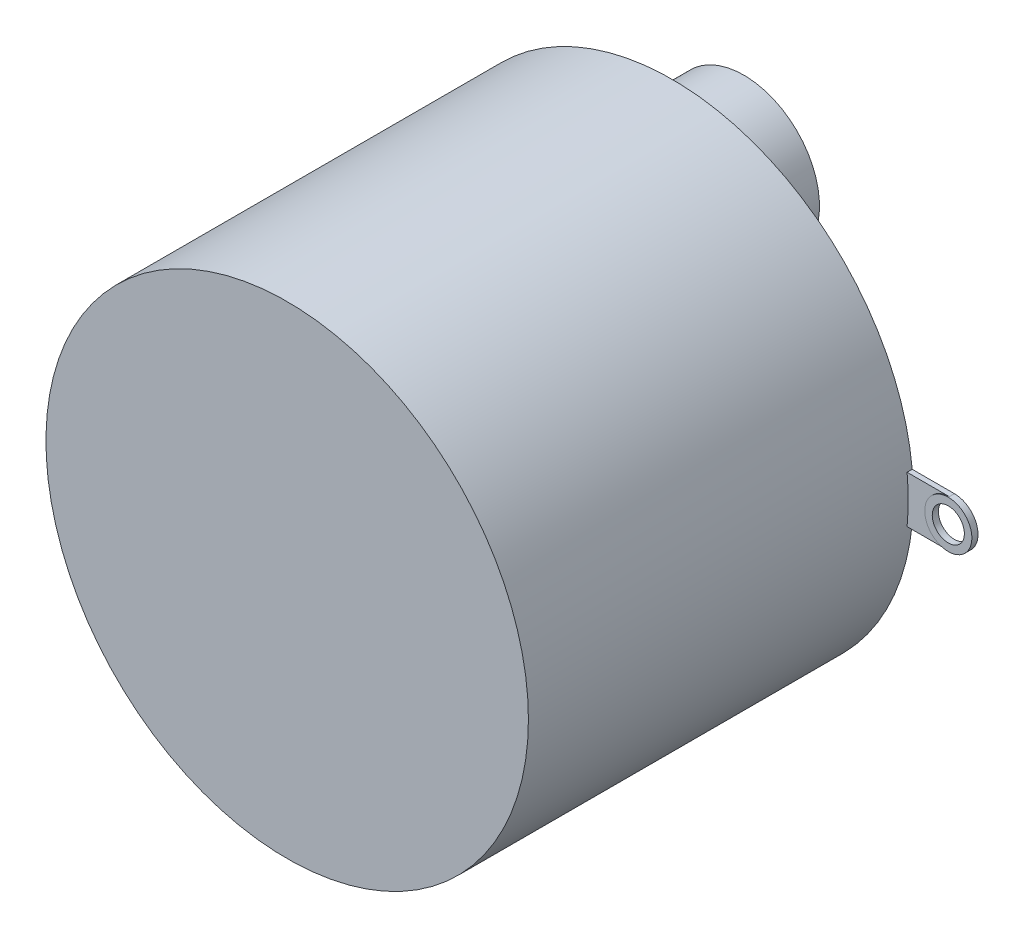
SolidWorks part; units mm, degrees
ref_plane "Front Plane" through (0, 0, 0) normal (0, 0, 1) x (1, 0, 0)
ref_plane "Top Plane" through (0, 0, 0) normal (0, 1, 0) x (1, 0, 0)
ref_plane "Right Plane" through (0, 0, 0) normal (1, 0, 0) x (0, 0, -1)
sketch "Sketch1" plane through (0, 0, 0) normal (0, 0, 1) x (1, 0, 0)
  circle A0 centre (0, 0) radius 11.938
extrude "Boss-Extrude1" add sketch "Sketch1" along normal blind 19.05 contours A0
sketch "Sketch2" plane through (0, 0, 0) normal (0, 0, -1) x (-1, 0, 0)
  line L0 (0, 0) -> (13.97, 0)
  line L1 (0, 0) -> (-13.97, 0)
  circle A0 centre (13.97, 0) radius 1.1775
  circle A1 centre (-13.97, 0) radius 1.1652
extrude "Boss-Extrude2" add sketch "Sketch2" against normal blind 0.3042 separate body
sketch "Sketch3" plane through (0, 0, 0) normal (0, 0, -1) x (-1, 0, 0)
  line L1 (-13.97, 1.1652) -> (14.14, 1.1652)
  line L2 (-13.97, 1.1652) -> (-13.97, -1.1652)
  line L3 (-13.97, -1.1652) -> (14.14, -1.1652)
  line L4 (14.14, 1.1652) -> (14.14, -1.1652)
  circle A0 centre (-13.97, 0) radius 1.1652 construction
  circle A1 centre (13.97, 0) radius 1.1775 construction
extrude "Boss-Extrude3" add sketch "Sketch3" against normal blind 0.254
sketch "Sketch4" plane through (0, 0, 0) normal (0, 0, -1) x (-1, 0, 0)
  circle A0 centre (-13.97, 0) radius 0.7952
extrude "Cut-Extrude1" cut sketch "Sketch4" against normal blind 0.9057
sketch "Sketch5" plane through (0, 0, 0) normal (0, 0, -1) x (-1, 0, 0)
  circle A0 centre (13.97, 0) radius 0.754
extrude "Cut-Extrude2" cut sketch "Sketch5" against normal blind 1.016
sketch "Sketch6" plane through (0, 0, 0) normal (0, 0, -1) x (-1, 0, 0)
  line L0 (0, 0) -> (0, 6.604)
  circle A0 centre (0, 6.604) radius 0.4708
extrude "Boss-Extrude4" add sketch "Sketch6" along normal blind 0.245
sketch "Sketch8" plane through (0, 0, -0.245) normal (0, 0, -1) x (-1, 0, 0)
  circle A0 centre (0, 6.604) radius 3.7432
extrude "Boss-Extrude5" add sketch "Sketch8" along normal blind 3.302 contours A0
